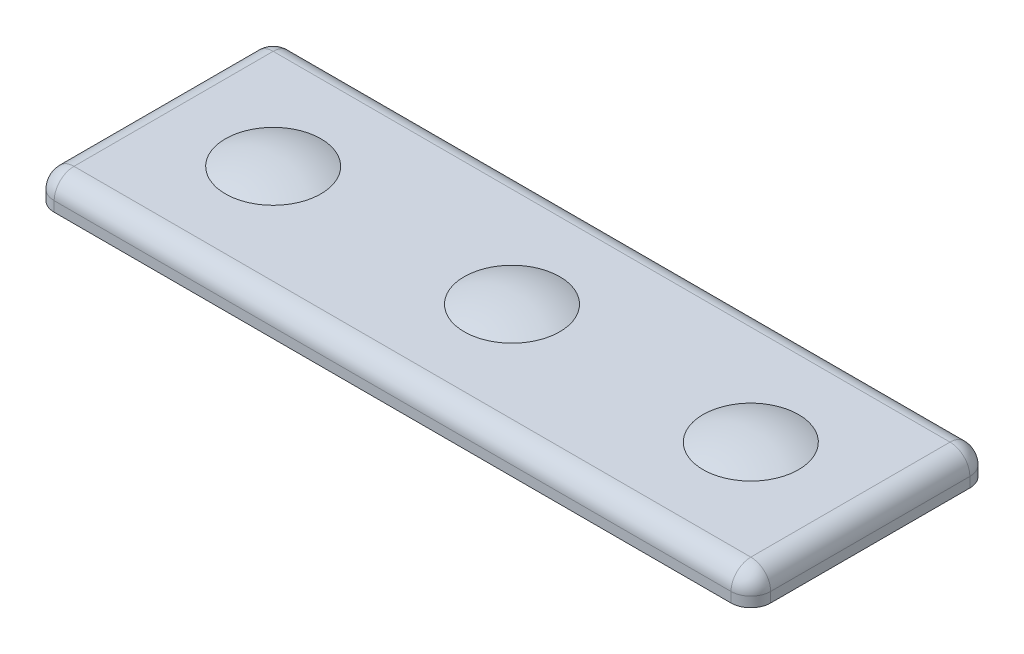
SolidWorks part; units mm, degrees
material "ABS"
ref_plane "Front Plane" through (0, 0, 0) normal (0, 0, 1) x (1, 0, 0)
ref_plane "Top Plane" through (0, 0, 0) normal (0, 1, 0) x (1, 0, 0)
ref_plane "Right Plane" through (0, 0, 0) normal (1, 0, 0) x (0, 0, -1)
sketch "Sketch1" plane through (0, 0, 0) normal (0, 1, 0) x (1, 0, 0)
  line L0 (-38.1, 0) -> (38.1, 0) construction
  line L1 (-25.4, -3.2639) -> (-25.4, 3.2639) construction
  line L3 (0, -12.7) -> (0, 12.7) construction
  point P4 (0, 0)
  point P8 (0, 0)
  point P11 (0, 12.7)
  point P15 (-25.4, 0)
  point P17 (0, 0)
sketch "Sketch2" plane through (0, 0, 0) normal (0, 0, 1) x (1, 0, 0)
  line L0 (-25.4, -7.0485) -> (-25.4, 7.0485) construction
  line L1 (-38.1, 0) -> (38.1, 0) construction
  line L2 (-20.32, 5.9954) -> (-30.48, 5.9954) construction
  line L3 (-22.352, -7.0485) -> (-28.448, -7.0485) construction
  line L4 (-23.7998, 0) -> (-27.0002, 0) construction
  point P0 (-25.4, 2.8204)
  point P3 (0, 0)
  point P9 (-25.4, 5.9954)
  point P10 (-25.4, -7.0485)
  point P11 (-25.4, -7.0485)
  point P17 (-25.4, 0)
  dimension "OAL" = 14.097
  dimension "Head Height" = 1.0531
  dimension "Cap Thickness" = 3.175
  dimension "Rivet Head Dea" = 10.16
  dimension "Rivet Dia" = 3.2004
  dimension "Rivet Flange Dia" = 6.096
sketch "Sketch3" plane through (0, 0, 0) normal (0, 1, 0) x (1, 0, 0)
  line L0 (0, -12.7) -> (0, 12.7) construction
  line L1 (38.1, -12.7) -> (-38.1, -12.7)
  line L2 (38.1, -12.7) -> (38.1, 12.7)
  line L3 (38.1, 12.7) -> (-38.1, 12.7)
  line L4 (-38.1, -12.7) -> (-38.1, 12.7)
  line L5 (38.1, -12.7) -> (-38.1, 12.7) construction
  line L6 (38.1, 12.7) -> (-38.1, -12.7) construction
  line L7 (0, -12.7) -> (0, 12.7) construction
  circle A1 centre (-25.4, 0) radius 3.2639
  circle A2 centre (25.4, 0) radius 3.2639
  circle A3 centre (0, 0) radius 3.2639
  point P0 (0, 0)
extrude "Boss-Extrude1" add sketch "Sketch3" against normal up to vertex from vertex
fillet "Fillet1" radius 2.1082 8 edges at (-38.1, 5.9954, 0) (0, 5.9954, -12.7) (38.1, 5.9954, 0) (0, 5.9954, 12.7) (38.1, 4.4079, 12.7) (38.1, 4.4079, -12.7) (-38.1, 4.4079, -12.7) (-38.1, 4.4079, 12.7)
sketch "Sketch5" plane through (0, 0, 0) normal (0, 0, 1) x (1, 0, 0)
  line L0 (-25.4, -7.0485) -> (-25.4, 7.0485) construction
  line L1 (-25.4, -7.0485) -> (-25.4, 7.0485) construction
  line L2 (-30.48, 5.9954) -> (-27.0002, 5.9954)
  line L3 (-20.32, 5.9954) -> (-30.48, 5.9954) construction
  line L4 (-27.0002, 5.9954) -> (-27.0002, 2.3966)
  line L5 (-27.0002, 2.3966) -> (-28.448, 2.9535)
  line L6 (-28.448, 2.9535) -> (-27.0002, 1.422)
  line L7 (-27.0002, 1.422) -> (-27.0002, 2.3966) construction
  line L8 (-27.0002, 1.422) -> (-27.0002, 0.914)
  line L9 (-27.0002, 0.914) -> (-28.448, 1.4709)
  line L10 (-28.448, 1.4709) -> (-27.0002, -0.0606)
  line L11 (-27.0002, -0.0606) -> (-27.0002, -0.5686)
  line L12 (-27.0002, -0.5686) -> (-28.448, -0.0117)
  line L13 (-28.448, -0.0117) -> (-27.0002, -1.5433)
  line L14 (-27.0002, -1.5433) -> (-27.0002, -2.0513)
  line L15 (-27.0002, -2.0513) -> (-28.448, -1.4943)
  line L16 (-28.448, -1.4943) -> (-27.0002, -3.0259)
  line L17 (-27.0002, -3.0259) -> (-27.0002, -3.5339)
  line L18 (-27.0002, -3.5339) -> (-28.448, -2.977)
  line L19 (-28.448, -2.977) -> (-27.0002, -4.5085)
  line L20 (-27.0002, -4.5085) -> (-27.0002, -5.0165) construction
  line L21 (-27.0002, -4.5085) -> (-28.448, -4.5085)
  line L22 (-28.448, -4.5085) -> (-27.0589, -6.0579)
  line L23 (-27.0589, -6.0579) -> (-27.0589, -6.3881)
  line L24 (-27.0589, -6.3881) -> (-27.1859, -6.3881)
  line L25 (-27.1859, -6.3881) -> (-26.5938, -7.0485)
  line L26 (-22.352, -7.0485) -> (-28.448, -7.0485) construction
  line L27 (-26.5938, -7.0485) -> (-25.4, -7.0485)
  line L28 (-25.4, -7.0485) -> (-25.4, 7.0485)
  arc A0 (-30.48, 5.9954) -> (-25.4, 7.0485) centre (-25.4, -5.7308) cw
  dimension "D6" = 0.6604
  dimension "D7" = 2.3876
  dimension "D8" = 0.127
  dimension "D9" = 1.8796
  dimension "D10" = 0.3302
  dimension "D2" = 0.508
  dimension "D3" = 25.57
  dimension "D4" = 111.04
  dimension "D11" = 5
revolve "Revolve1" add sketch "Sketch5" angle 360 about L0
sketch "Sketch6" plane through (0, 5.9954, 0) normal (0, -1, 0) x (1, 0, 0)
  line L0 (-25.4, 0) -> (-25.4, 5.08) construction
  line L1 (-23.7537, 5.08) -> (-27.0463, 5.08)
  line L2 (-27.0463, 5.08) -> (-26.035, 1.4688)
  line L3 (-23.7537, 5.08) -> (-24.765, 1.4688)
  circle A0 centre (-25.4, 0) radius 5.08 construction
  circle A1 centre (-25.4, 0) radius 1.6002 construction
  arc A2 (-24.765, 1.4688) -> (-26.035, 1.4688) centre (-25.4, 0) ccw
  dimension "D1" = 1.27
  dimension "D2" = 31.29
extrude "Cut-Extrude1" cut sketch "Sketch6" along normal up to surface (12.3835 mm away) up to face at (-25.4, -6.3881, -1.7859)
pattern_linear "LPattern1" count 3 spacing 25.4 along (1, 0, 0) of bodies 108
equation "\"D10@Sketch5\"=\"D6@Sketch5\"/2"
equation "\"D3@LPattern1\"=\"Hole Spacing@Sketch1\""
